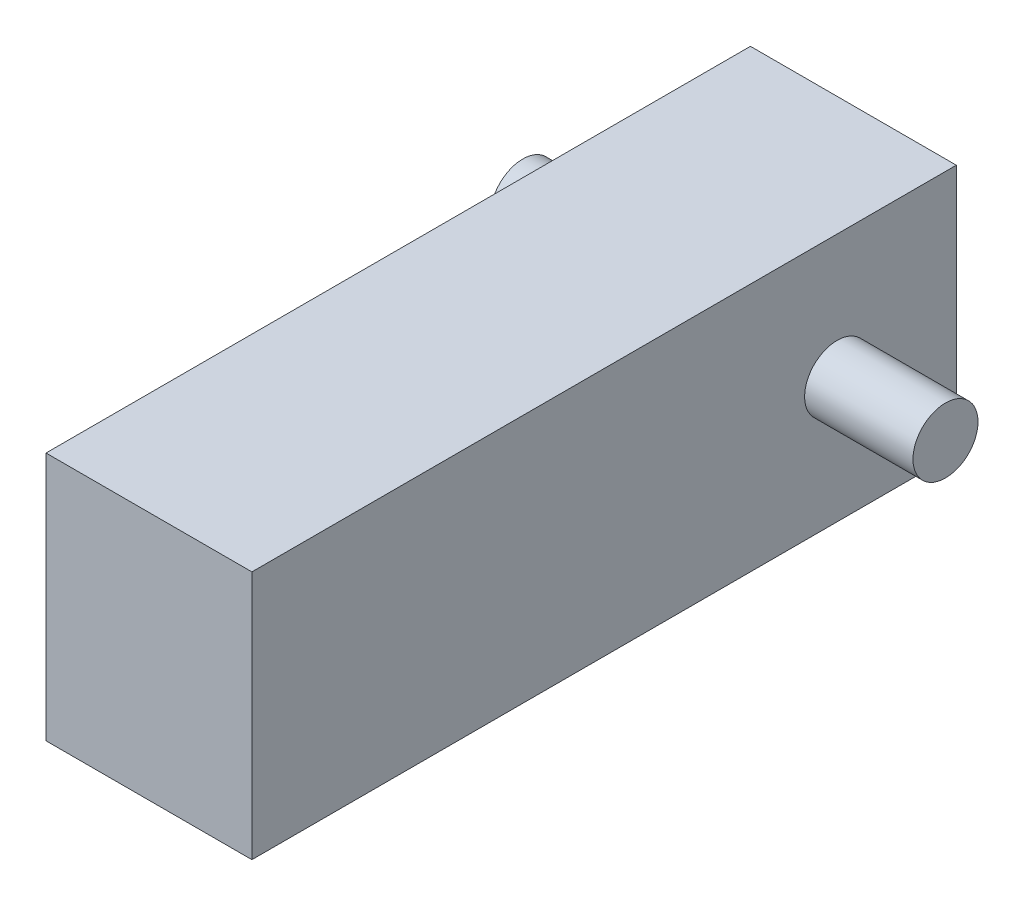
SolidWorks part; units mm, degrees
ref_plane "Alzado" through (0, 0, 0) normal (0, 0, 1) x (1, 0, 0)
ref_plane "Planta" through (0, 0, 0) normal (0, 1, 0) x (1, 0, 0)
ref_plane "Vista lateral" through (0, 0, 0) normal (1, 0, 0) x (0, 0, -1)
sketch "Croquis1" plane through (0, 0, 0) normal (0, 1, 0) x (1, 0, 0)
  line L1 (-9.5, 32.5) -> (9.5, 32.5)
  line L2 (-9.5, 32.5) -> (-9.5, -32.5)
  line L3 (-9.5, -32.5) -> (9.5, -32.5)
  line L4 (9.5, 32.5) -> (9.5, -32.5)
  line L5 (-9.5, 32.5) -> (9.5, -32.5) construction
  line L6 (-9.5, -32.5) -> (9.5, 32.5) construction
  point P0 (0, 0)
  dimension "D1" = 19
  dimension "D2" = 65
extrude "Saliente-Extruir1" add sketch "Croquis1" along normal blind 23
sketch "Croquis2" plane through (9.5, 0, 0) normal (1, 0, 0) x (0, 0, -1)
  circle A0 centre (21.5, 11.5) radius 3
extrude "Saliente-Extruir2" add sketch "Croquis2" along normal blind 10
sketch "Croquis3" plane through (19.5, 0, 0) normal (1, 0, 0) x (0, 0, -1)
  circle A0 centre (21.5, 11.5) radius 3
extrude "Saliente-Extruir3" add sketch "Croquis3" against normal blind 39
sketch "Croquis4" plane through (-9.5, 0, 0) normal (-1, 0, 0) x (0, 0, 1)
  circle A0 centre (-9.5, 11.9628) radius 1.5
  circle A1 centre (-21.5, 11.5) radius 3 construction
  dimension "D2" = 3
  dimension "D1" = 12
extrude "Saliente-Extruir4" add sketch "Croquis4" along normal blind 1
